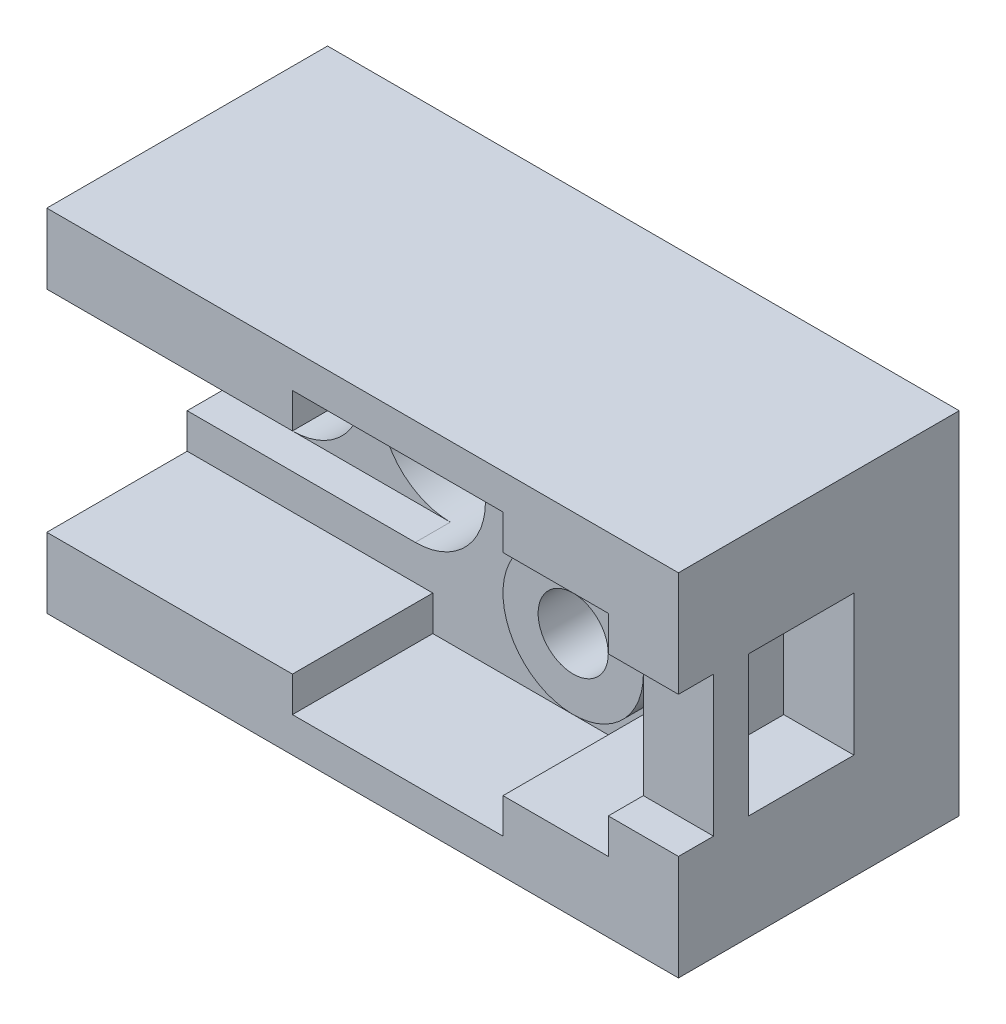
SolidWorks part; units mm, degrees
ref_plane "Front Plane" through (0, 0, 0) normal (0, 0, 1) x (1, 0, 0)
ref_plane "Top Plane" through (0, 0, 0) normal (0, 1, 0) x (1, 0, 0)
ref_plane "Right Plane" through (0, 0, 0) normal (1, 0, 0) x (0, 0, -1)
sketch "Sketch1" plane through (0, 0, 0) normal (0, 0, 1) x (1, 0, 0)
  line L1 (0, 0) -> (180, 0)
  line L2 (0, 0) -> (0, 100)
  line L3 (0, 100) -> (180, 100)
  line L4 (180, 0) -> (180, 100)
  dimension "D1" = 100
  dimension "D2" = 180
extrude "Boss-Extrude1" add sketch "Sketch1" along normal blind 80
sketch "Sketch2" plane through (0, 0, 80) normal (0, 0, 1) x (1, 0, 0)
  line L0 (0, 70) -> (20, 70)
  line L1 (0, 100) -> (0, 0) construction
  line L2 (0, 30) -> (20, 30)
  line L3 (0, 70) -> (0, 30)
  arc A0 (20, 70) -> (20, 30) centre (20, 50) cw
  dimension "D4" = 20
  dimension "D1" = 20
  dimension "D2" = 20
  dimension "D3" = 40
  dimension "D5" = 30
extrude "Cut-Extrude1" cut sketch "Sketch2" against normal blind 80
sketch "Sketch3" plane through (0, 0, 0) normal (0, 0, -1) x (-1, 0, 0)
  circle A0 centre (-65, 50) radius 5
  dimension "D1" = 10
  dimension "D2" = 50
  dimension "D3" = 65
extrude "Cut-Extrude2" cut sketch "Sketch3" against normal blind 20
sketch "Sketch4" plane through (0, 0, 0) normal (0, 0, -1) x (-1, 0, 0)
  circle A0 centre (-130, 50) radius 10
  dimension "D1" = 20
  dimension "D2" = 50
  dimension "D3" = 50
extrude "Cut-Extrude3" cut sketch "Sketch4" against normal blind 60
sketch "Sketch5" plane through (0, 0, 80) normal (0, 0, 1) x (1, 0, 0)
  circle A0 centre (65, 50) radius 20
  dimension "D1" = 40
  dimension "D2" = 50
  dimension "D3" = 65
extrude "Cut-Extrude4" cut sketch "Sketch5" against normal blind 60
sketch "Sketch6" plane through (0, 0, 80) normal (0, 0, 1) x (1, 0, 0)
  circle A0 centre (130, 50) radius 20
  circle A1 centre (65, 50) radius 5 construction
  point P2 (0, 0)
  dimension "D1" = 40
  dimension "D2" = 50
  dimension "D3" = 50
extrude "Cut-Extrude5" cut sketch "Sketch6" against normal blind 50
sketch "Sketch7" plane through (0, 0, 80) normal (0, 0, 1) x (1, 0, 0)
  line L0 (20, 70) -> (65, 70)
  line L1 (20, 30) -> (65, 30)
  circle A0 centre (65, 50) radius 20 construction
  arc A1 (65, 70) -> (65, 30) centre (65, 50) ccw
  arc A2 (20, 70) -> (20, 30) centre (20, 50) cw
  arc A3 (20, 30) -> (20, 70) centre (20, 50) ccw construction
  dimension "D1" = 20
extrude "Cut-Extrude6" cut sketch "Sketch7" against normal blind 50
sketch "Sketch8" plane through (180, 0, 0) normal (1, 0, 0) x (0, 0, -1)
  line L0 (-80, 0) -> (-80, 100) construction
  line L1 (-80, 70) -> (-70, 70)
  line L2 (-80, 70) -> (-80, 30)
  line L3 (-80, 30) -> (-70, 30)
  line L4 (-70, 70) -> (-70, 30)
  dimension "D1" = 10
  dimension "D2" = 40
  dimension "D3" = 30
extrude "Cut-Extrude7" cut sketch "Sketch8" against normal blind 207
sketch "Sketch9" plane through (0, 0, 80) normal (0, 0, 1) x (1, 0, 0)
  line L0 (180, 70) -> (160, 70)
  line L1 (180, 70) -> (0, 70) construction
  line L2 (160, 70) -> (160, 80)
  line L3 (160, 80) -> (130, 80)
  line L4 (130, 80) -> (130, 90)
  line L5 (130, 90) -> (70, 90)
  line L6 (70, 90) -> (70, 80)
  line L7 (0, 80) -> (0, 70)
  line L8 (0, 100) -> (0, 70) construction
  line L9 (0, 70) -> (160, 70)
  line L10 (0, 80) -> (70, 80)
  line M1 (0, 70) -> (180, 70)
  line M4 (0, 100) -> (0, 70)
  dimension "D1" = 20
  dimension "D2" = 10
  dimension "D3" = 30
  dimension "D4" = 10
  dimension "D5" = 10
  dimension "D6" = 60
extrude "Cut-Extrude8" cut sketch "Sketch9" against normal blind 10 contours L10 L2 L3 L4 L5 L6 M4 M1
sketch "Sketch10" plane through (0, 0, 80) normal (0, 0, 1) x (1, 0, 0)
  line L0 (180, 30) -> (160, 30)
  line L1 (0, 30) -> (180, 30) construction
  line L2 (160, 30) -> (160, 20)
  line L3 (160, 20) -> (130, 20)
  line L4 (130, 20) -> (130, 10)
  line L5 (130, 10) -> (70, 10)
  line L6 (70, 10) -> (70, 20)
  line L7 (70, 20) -> (0, 20)
  line L8 (0, 30) -> (0, 0) construction
  line L9 (0, 20) -> (0, 30)
  line L10 (0, 30) -> (160, 30)
  line M2 (180, 30) -> (0, 30)
  line M3 (0, 30) -> (0, 0)
  dimension "D1" = 20
  dimension "D2" = 10
  dimension "D3" = 30
  dimension "D4" = 10
  dimension "D5" = 60
  dimension "D6" = 10
extrude "Cut-Extrude9" cut sketch "Sketch10" against normal blind 10 contours L7 L6 L5 L4 L3 L2 M2 M3
sketch "Sketch11" plane through (0, 0, 70) normal (0, 0, 1) x (1, 0, 0)
  line L1 (180, 70) -> (160, 70)
  line L2 (180, 70) -> (180, 30)
  line L3 (180, 30) -> (160, 30)
  line L4 (160, 70) -> (160, 30)
extrude "Cut-Extrude10" cut sketch "Sketch11" against normal blind 30
sketch "Sketch12" plane through (0, 0, 30) normal (0, 0, 1) x (1, 0, 0)
  circle A0 centre (130, 50) radius 10
  circle A1 centre (130, 50) radius 20
  dimension "D1" = 20
  dimension "D2" = 40
extrude "Boss-Extrude3" add sketch "Sketch12" along normal blind 30
sketch "Sketch13" plane through (0, 0, 70) normal (0, 0, 1) x (1, 0, 0)
  line L0 (0, 70) -> (0, 80)
  line L1 (0, 80) -> (70, 80)
  line L2 (70, 80) -> (70, 90)
  line L3 (70, 90) -> (130, 90)
  line L4 (130, 90) -> (130, 80)
  line L5 (130, 80) -> (160, 80)
  line L6 (160, 80) -> (160, 20)
  line L7 (160, 20) -> (130, 20)
  line L8 (130, 20) -> (130, 10)
  line L9 (130, 10) -> (70, 10)
  line L10 (70, 10) -> (70, 20)
  line L11 (70, 20) -> (0, 20)
  line L12 (70, 20) -> (0, 20) construction
  line L13 (0, 30) -> (0, 20) construction
  line L14 (0, 20) -> (0, 30)
  line L15 (0, 30) -> (65, 30)
  line L16 (65, 30) -> (0, 30) construction
  line L17 (0, 70) -> (65, 70)
  line L18 (0, 70) -> (65, 70) construction
  line L19 (0, 80) -> (0, 70)
  arc A0 (65, 30) -> (65, 70) centre (65, 50) ccw construction
  arc A1 (65, 70) -> (65, 30) centre (65, 50) cw
  circle M1 centre (130, 50) radius 20
  line M2 (160, 20) -> (160, 30)
  line M3 (160, 30) -> (160, 70)
  line M4 (160, 70) -> (160, 80)
  line M5 (160, 80) -> (130, 80)
  line M6 (130, 80) -> (130, 90)
  line M7 (130, 90) -> (70, 90)
  line M8 (70, 90) -> (70, 80)
  line M9 (70, 80) -> (0, 80)
  line M10 (0, 80) -> (0, 70)
  line M11 (0, 70) -> (65, 70)
  arc M12 (65, 70) -> (65, 30) centre (65, 50) cw
  line M13 (65, 30) -> (0, 30)
  line M14 (0, 30) -> (0, 20)
  line M15 (0, 20) -> (70, 20)
  line M16 (70, 20) -> (70, 10)
  line M17 (70, 10) -> (130, 10)
  line M18 (130, 10) -> (130, 20)
  line M19 (130, 20) -> (160, 20)
extrude "Cut-Extrude11" cut sketch "Sketch13" against normal blind 30 contours M19 M2 M3 M4 M5 M6 M7 M8 M9 M10 M11 M12 M13 M14 M15 M16 M17 M18 M1
sketch "Sketch14" plane through (0, 0, 40) normal (0, 0, 1) x (1, 0, 0)
  line L1 (180, 70) -> (160, 70)
  line L2 (180, 70) -> (180, 30)
  line L3 (180, 30) -> (160, 30)
  line L4 (160, 70) -> (160, 30)
extrude "Cut-Extrude12" cut sketch "Sketch14" against normal blind 10
sketch "Sketch15" plane through (160, 0, 0) normal (-1, 0, 0) x (0, 0, 1)
  line L0 (70, 70) -> (70, 30)
  line L1 (40, 70) -> (80, 70) construction
  line L2 (40, 30) -> (80, 30) construction
  line L3 (70, 30) -> (60, 30)
  line L4 (60, 30) -> (60, 70)
  line L5 (60, 70) -> (70, 70)
  dimension "D1" = 10
extrude "Boss-Extrude5" add sketch "Sketch15" against normal blind 20
